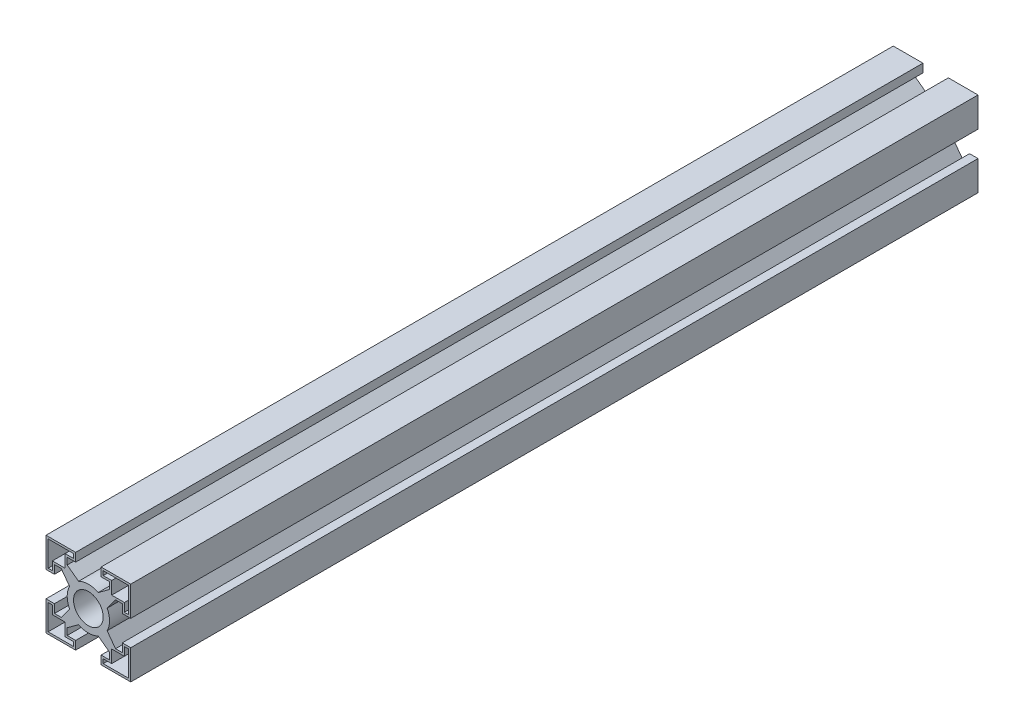
SolidWorks part; units mm, degrees
ref_plane "Plan de face" through (0, 0, 0) normal (0, 0, 1) x (1, 0, 0)
ref_plane "Plan de dessus" through (0, 0, 0) normal (0, 1, 0) x (1, 0, 0)
ref_plane "Plan de droite" through (0, 0, 0) normal (1, 0, 0) x (0, 0, -1)
sketch "Esquisse1" plane through (0, 0, 0) normal (0, 0, 1) x (1, 0, 0)
  line L5 (-5, 5) -> (-5, 1.5)
  line L22 (5, -5) -> (-5, -5) construction
  line L23 (5, -5) -> (5, 5) construction
  line L24 (5, 5) -> (-5, 5) construction
  line L25 (-5, -5) -> (-5, 5) construction
  line L26 (5, -5) -> (-5, 5) construction
  line L27 (5, 5) -> (-5, -5) construction
  line L28 (-5, 1.5) -> (-4, 1.5)
  line L29 (-4, 1.5) -> (-4, 2.5)
  line L30 (-4, 2.5) -> (-2.5, 2.5)
  line L79 (-2.5, 2.5) -> (-2.5, 4)
  line L80 (-2.5, 4) -> (-1.5, 4)
  line L82 (-1.5, 4) -> (-1.5, 5)
  line L85 (-1.5, 5) -> (-5, 5)
  line L86 (-4.75, 4.75) -> (-4.75, 1.75)
  line L87 (-4.75, 1.75) -> (-4.25, 1.75)
  line L88 (-4.25, 1.75) -> (-4.25, 2.75)
  line L89 (-4.25, 2.75) -> (-2.75, 2.75)
  line L90 (-2.75, 2.75) -> (-2.75, 4.25)
  line L92 (-2.75, 4.25) -> (-1.75, 4.25)
  line L93 (-1.75, 4.25) -> (-1.75, 4.75)
  line L94 (-1.75, 4.75) -> (-4.75, 4.75)
  line L95 (5, 5) -> (1.5, 5)
  line L96 (1.5, 5) -> (1.5, 4)
  line L97 (1.5, 4) -> (2.5, 4)
  line L98 (2.5, 4) -> (2.5, 2.5)
  line L99 (2.5, 2.5) -> (4, 2.5)
  line L100 (4, 2.5) -> (4, 1.5)
  line L101 (4, 1.5) -> (5, 1.5)
  line L102 (5, 1.5) -> (5, 5)
  line L103 (4.75, 4.75) -> (1.75, 4.75)
  line L104 (1.75, 4.75) -> (1.75, 4.25)
  line L105 (1.75, 4.25) -> (2.75, 4.25)
  line L106 (2.75, 4.25) -> (2.75, 2.75)
  line L107 (2.75, 2.75) -> (4.25, 2.75)
  line L108 (4.25, 2.75) -> (4.25, 1.75)
  line L109 (4.25, 1.75) -> (4.75, 1.75)
  line L110 (4.75, 1.75) -> (4.75, 4.75)
  line L111 (5, -5) -> (5, -1.5)
  line L112 (5, -1.5) -> (4, -1.5)
  line L113 (4, -1.5) -> (4, -2.5)
  line L114 (4, -2.5) -> (2.5, -2.5)
  line L115 (2.5, -2.5) -> (2.5, -4)
  line L116 (2.5, -4) -> (1.5, -4)
  line L117 (1.5, -4) -> (1.5, -5)
  line L118 (1.5, -5) -> (5, -5)
  line L119 (4.75, -4.75) -> (4.75, -1.75)
  line L120 (4.75, -1.75) -> (4.25, -1.75)
  line L121 (4.25, -1.75) -> (4.25, -2.75)
  line L122 (4.25, -2.75) -> (2.75, -2.75)
  line L123 (2.75, -2.75) -> (2.75, -4.25)
  line L124 (2.75, -4.25) -> (1.75, -4.25)
  line L125 (1.75, -4.25) -> (1.75, -4.75)
  line L126 (1.75, -4.75) -> (4.75, -4.75)
  line L127 (-5, -5) -> (-1.5, -5)
  line L128 (-1.5, -5) -> (-1.5, -4)
  line L129 (-1.5, -4) -> (-2.5, -4)
  line L130 (-2.5, -4) -> (-2.5, -2.5)
  line L131 (-2.5, -2.5) -> (-4, -2.5)
  line L132 (-4, -2.5) -> (-4, -1.5)
  line L133 (-4, -1.5) -> (-5, -1.5)
  line L134 (-5, -1.5) -> (-5, -5)
  line L135 (-4.75, -4.75) -> (-1.75, -4.75)
  line L136 (-1.75, -4.75) -> (-1.75, -4.25)
  line L137 (-1.75, -4.25) -> (-2.75, -4.25)
  line L138 (-2.75, -4.25) -> (-2.75, -2.75)
  line L139 (-2.75, -2.75) -> (-4.25, -2.75)
  line L140 (-4.25, -2.75) -> (-4.25, -1.75)
  line L141 (-4.25, -1.75) -> (-4.75, -1.75)
  line L142 (-4.75, -1.75) -> (-4.75, -4.75)
  line L143 (-3.2071, 2.5) -> (-2.2167, 1.156)
  line L144 (-2.5, 3.2071) -> (-1.156, 2.2167)
  line L145 (-2.2167, 1.156) -> (-1.156, 2.2167) construction
  line L146 (-2.5, 3.2071) -> (-3.2071, 2.5) construction
  line L147 (3.2071, 2.5) -> (2.2167, 1.156)
  line L148 (2.5, 3.2071) -> (1.156, 2.2167)
  line L149 (2.5, -3.2071) -> (1.156, -2.2167)
  line L150 (3.2071, -2.5) -> (2.2167, -1.156)
  line L151 (-3.2071, -2.5) -> (-2.2167, -1.156)
  line L152 (-2.5, -3.2071) -> (-1.156, -2.2167)
  circle A2 centre (0, 0) radius 1.75
  circle A3 centre (0, 0) radius 2.5
  point P73 (0, 0)
  point P78 (-2.8536, 2.8536)
  point P79 (-1.6863, 1.6863)
  point P91 (0, 0)
  dimension "D2" = 3.5
  dimension "D3" = 10
  dimension "D1" = 5
  dimension "D4" = 3.5
  dimension "D5" = 1
  dimension "D6" = 1.5
  dimension "D7" = 0.25
  dimension "D8" = 4
  dimension "D9" = 1
  dimension "D10" = 1.5
extrude "Boss.-Extru.1" add sketch "Esquisse1" along normal blind 100
